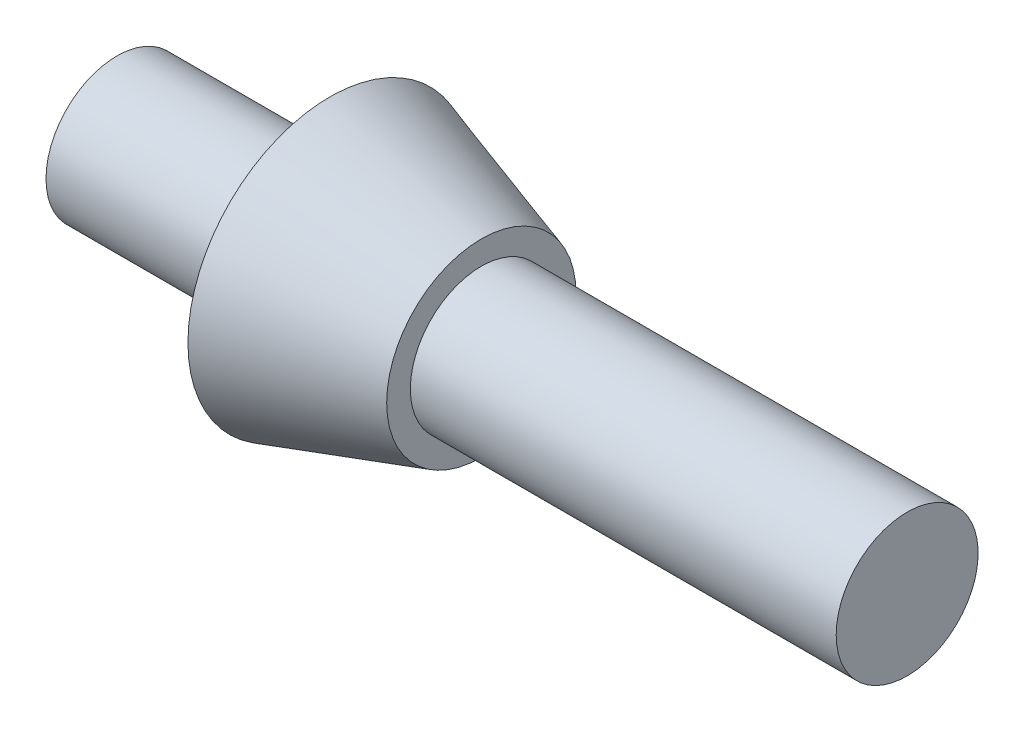
SolidWorks part; units mm, degrees
material "ABS PC"
ref_plane "前视基准面" through (0, 0, 0) normal (0, 0, 1) x (1, 0, 0)
ref_plane "上视基准面" through (0, 0, 0) normal (0, 1, 0) x (1, 0, 0)
ref_plane "右视基准面" through (0, 0, 0) normal (1, 0, 0) x (0, 0, -1)
sketch "草图1" plane through (0, 0, 0) normal (0, 0, 1) x (1, 0, 0)
  line L0 (-51.7302, 0) -> (48.3656, 0) construction
  line L1 (-9.7463, 1.5) -> (-5.2463, 1.5)
  line L2 (-5.2463, 1.5) -> (-5.2463, 3)
  line L3 (-5.2463, 3) -> (-2.0463, 2)
  line L4 (-2.0463, 2) -> (-2.0463, 1.5)
  line L5 (-2.0463, 1.5) -> (6.9537, 1.5)
  line L6 (6.9537, 1.5) -> (6.9537, 0)
  line L7 (-9.7463, 1.5) -> (-9.7463, 0)
  line L8 (6.9537, 0) -> (-9.7463, 0)
  dimension "D1" = 3
  dimension "D2" = 3
  dimension "D3" = 4
  dimension "D4" = 6
  dimension "D5" = 9
  dimension "D6" = 4.5
  dimension "D7" = 3.2
revolve "旋转1" add sketch "草图1" angle 360 about L0
